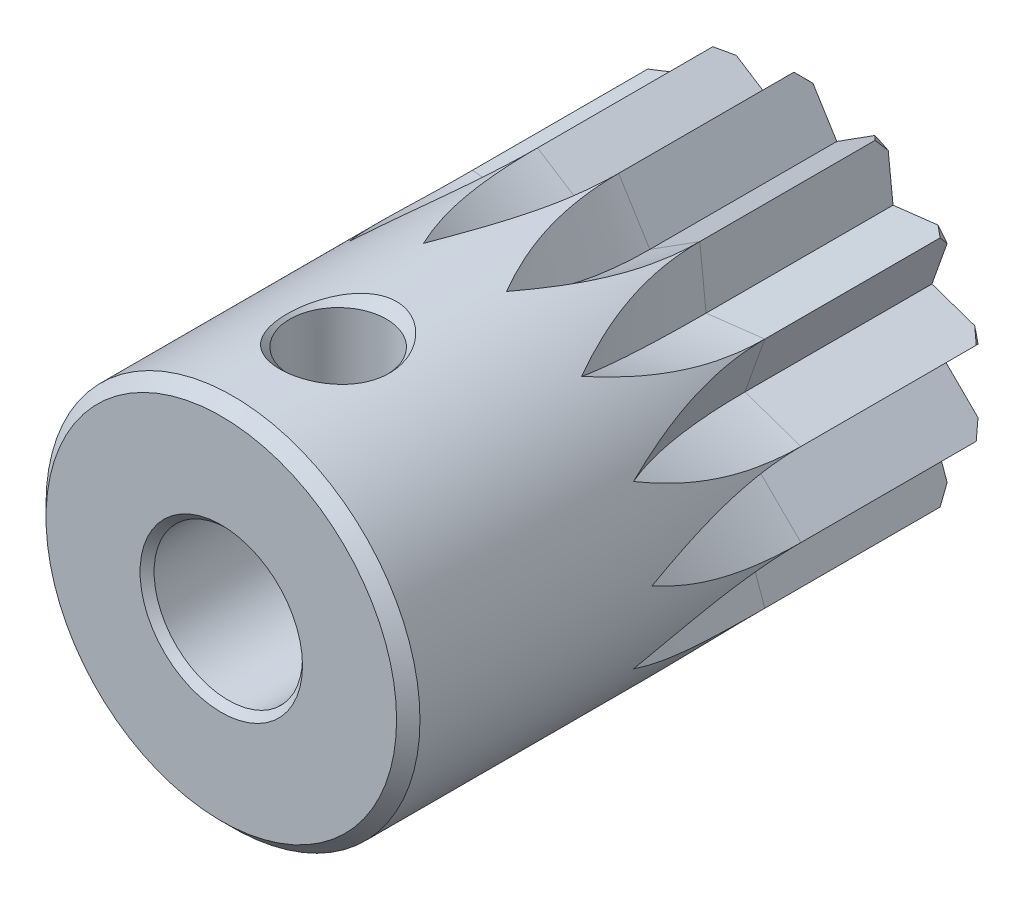
SolidWorks part; units mm, degrees
ref_plane "Front Plane" through (0, 0, 0) normal (0, 0, 1) x (1, 0, 0)
ref_plane "Top Plane" through (0, 0, 0) normal (0, 1, 0) x (1, 0, 0)
ref_plane "Right Plane" through (0, 0, 0) normal (1, 0, 0) x (0, 0, -1)
ref_plane "Plane1" through (0, 0, 0) normal (1, 0, 0) x (0, 0, -1)
sketch "Sketch1" plane through (0, 0, 0) normal (1, 0, 0) x (0, 0, -1)
  line L0 (-25, 3.475) -> (-24.7, 3.175)
  line L1 (-24.7, 3.175) -> (-0.3, 3.175)
  line L2 (-0.3, 3.175) -> (0, 3.475)
  line L3 (0, 3.475) -> (0, 7.5)
  line L4 (0, 7.5) -> (-0.5, 8)
  line L5 (-0.5, 8) -> (-24.5, 8)
  line L6 (-24.5, 8) -> (-25, 7.5)
  line L7 (-25, 7.5) -> (-25, 3.475)
  line L8 (0, 0) -> (-25, 0) construction
revolve "Revolve1" add sketch "Sketch1" angle 360 about L8
ref_plane "Plane2" through (0, 0, 8) normal (0, 0, 1) x (1, 0, 0)
sketch "Sketch2" plane through (0, 0, 8) normal (0, 0, 1) x (1, 0, 0)
  line L0 (-7.7994, 1.7802) -> (-6, 0)
  line L1 (-6, 0) -> (-7.7994, -1.7802)
  line L2 (-7.7994, -1.7802) -> (-5.4058, -2.6033)
  line L3 (-5.4058, -2.6033) -> (-6.2547, -4.9879)
  line L4 (-6.2547, -4.9879) -> (-3.7409, -4.691)
  line L5 (-3.7409, -4.691) -> (-3.4711, -7.2078)
  line L6 (-3.4711, -7.2078) -> (-1.3351, -5.8496)
  line L7 (-1.3351, -5.8496) -> (0, -8)
  line L8 (0, -8) -> (1.3351, -5.8496)
  line L9 (1.3351, -5.8496) -> (3.4711, -7.2078)
  line L10 (3.4711, -7.2078) -> (3.7409, -4.691)
  line L11 (3.7409, -4.691) -> (6.2547, -4.9879)
  line L12 (6.2547, -4.9879) -> (5.4058, -2.6033)
  line L13 (5.4058, -2.6033) -> (7.7994, -1.7802)
  line L14 (7.7994, -1.7802) -> (6, 0)
  line L15 (6, 0) -> (7.7994, 1.7802)
  line L16 (7.7994, 1.7802) -> (5.4058, 2.6033)
  line L17 (5.4058, 2.6033) -> (6.2547, 4.9879)
  line L18 (6.2547, 4.9879) -> (3.7409, 4.691)
  line L19 (3.7409, 4.691) -> (3.4711, 7.2078)
  line L20 (3.4711, 7.2078) -> (1.3351, 5.8496)
  line L21 (1.3351, 5.8496) -> (0, 8)
  line L22 (0, 8) -> (-1.3351, 5.8496)
  line L23 (-1.3351, 5.8496) -> (-3.4711, 7.2078)
  line L24 (-3.4711, 7.2078) -> (-3.7409, 4.691)
  line L25 (-3.7409, 4.691) -> (-6.2547, 4.9879)
  line L26 (-6.2547, 4.9879) -> (-5.4058, 2.6033)
  line L27 (-5.4058, 2.6033) -> (-7.7994, 1.7802)
  circle A0 centre (0, 0) radius 16
extrude "Cut-Extrude1" cut sketch "Sketch2" against normal blind 8
ref_plane "Plane3" through (0, 0, 8) normal (0, 0, 1) x (1, 0, 0)
sketch "Sketch3" plane through (0, 0, 8) normal (0, 0, 1) x (1, 0, 0)
  line L0 (-2.2252, 17.7493) -> (0, 8)
  line L1 (0, 8) -> (-1.3351, 5.8496)
  line L2 (-1.3351, 5.8496) -> (-3.4711, 7.2078)
  line L3 (-3.4711, 7.2078) -> (-5.6963, 16.957)
  line L4 (-5.6963, 16.957) -> (-2.2252, 17.7493)
  line L5 (-5.6963, 16.957) -> (-2.2252, 17.7493) construction
revolve "Cut-Revolve1" cut sketch "Sketch3" angle 360 about L5
ref_plane "Plane4" through (0, 0, 8) normal (0, 0, 1) x (1, 0, 0)
sketch "Sketch4" plane through (0, 0, 8) normal (0, 0, 1) x (1, 0, 0)
  line L0 (5.6963, 16.957) -> (3.4711, 7.2078)
  line L1 (3.4711, 7.2078) -> (1.3351, 5.8496)
  line L2 (1.3351, 5.8496) -> (0, 8)
  line L3 (0, 8) -> (2.2252, 17.7493)
  line L4 (2.2252, 17.7493) -> (5.6963, 16.957)
  line L5 (2.2252, 17.7493) -> (5.6963, 16.957) construction
revolve "Cut-Revolve2" cut sketch "Sketch4" angle 360 about L5
ref_plane "Plane5" through (0, 0, 8) normal (0, 0, 1) x (1, 0, 0)
sketch "Sketch5" plane through (0, 0, 8) normal (0, 0, 1) x (1, 0, 0)
  line L0 (12.4895, 12.8062) -> (6.2547, 4.9879)
  line L1 (6.2547, 4.9879) -> (3.7409, 4.691)
  line L2 (3.7409, 4.691) -> (3.4711, 7.2078)
  line L3 (3.4711, 7.2078) -> (9.706, 15.0261)
  line L4 (9.706, 15.0261) -> (12.4895, 12.8062)
  line L5 (9.706, 15.0261) -> (12.4895, 12.8062) construction
revolve "Cut-Revolve3" cut sketch "Sketch5" angle 360 about L5
ref_plane "Plane6" through (0, 0, 8) normal (0, 0, 1) x (1, 0, 0)
sketch "Sketch6" plane through (0, 0, 8) normal (0, 0, 1) x (1, 0, 0)
  line L0 (16.8091, 6.119) -> (7.7994, 1.7802)
  line L1 (7.7994, 1.7802) -> (5.4058, 2.6033)
  line L2 (5.4058, 2.6033) -> (6.2547, 4.9879)
  line L3 (6.2547, 4.9879) -> (15.2643, 9.3268)
  line L4 (15.2643, 9.3268) -> (16.8091, 6.119)
  line L5 (15.2643, 9.3268) -> (16.8091, 6.119) construction
revolve "Cut-Revolve4" cut sketch "Sketch6" angle 360 about L5
ref_plane "Plane7" through (0, 0, 8) normal (0, 0, 1) x (1, 0, 0)
sketch "Sketch7" plane through (0, 0, 8) normal (0, 0, 1) x (1, 0, 0)
  line L0 (17.7994, -1.7802) -> (7.7994, -1.7802)
  line L1 (7.7994, -1.7802) -> (6, 0)
  line L2 (6, 0) -> (7.7994, 1.7802)
  line L3 (7.7994, 1.7802) -> (17.7994, 1.7802)
  line L4 (17.7994, 1.7802) -> (17.7994, -1.7802)
  line L5 (17.7994, 1.7802) -> (17.7994, -1.7802) construction
revolve "Cut-Revolve5" cut sketch "Sketch7" angle 360 about L5
ref_plane "Plane8" through (0, 0, 8) normal (0, 0, 1) x (1, 0, 0)
sketch "Sketch8" plane through (0, 0, 8) normal (0, 0, 1) x (1, 0, 0)
  line L0 (15.2643, -9.3268) -> (6.2547, -4.9879)
  line L1 (6.2547, -4.9879) -> (5.4058, -2.6033)
  line L2 (5.4058, -2.6033) -> (7.7994, -1.7802)
  line L3 (7.7994, -1.7802) -> (16.8091, -6.119)
  line L4 (16.8091, -6.119) -> (15.2643, -9.3268)
  line L5 (16.8091, -6.119) -> (15.2643, -9.3268) construction
revolve "Cut-Revolve6" cut sketch "Sketch8" angle 360 about L5
ref_plane "Plane9" through (0, 0, 8) normal (0, 0, 1) x (1, 0, 0)
sketch "Sketch9" plane through (0, 0, 8) normal (0, 0, 1) x (1, 0, 0)
  line L0 (9.706, -15.0261) -> (3.4711, -7.2078)
  line L1 (3.4711, -7.2078) -> (3.7409, -4.691)
  line L2 (3.7409, -4.691) -> (6.2547, -4.9879)
  line L3 (6.2547, -4.9879) -> (12.4895, -12.8062)
  line L4 (12.4895, -12.8062) -> (9.706, -15.0261)
  line L5 (12.4895, -12.8062) -> (9.706, -15.0261) construction
revolve "Cut-Revolve7" cut sketch "Sketch9" angle 360 about L5
ref_plane "Plane10" through (0, 0, 8) normal (0, 0, 1) x (1, 0, 0)
sketch "Sketch10" plane through (0, 0, 8) normal (0, 0, 1) x (1, 0, 0)
  line L0 (2.2252, -17.7493) -> (0, -8)
  line L1 (0, -8) -> (1.3351, -5.8496)
  line L2 (1.3351, -5.8496) -> (3.4711, -7.2078)
  line L3 (3.4711, -7.2078) -> (5.6963, -16.957)
  line L4 (5.6963, -16.957) -> (2.2252, -17.7493)
  line L5 (5.6963, -16.957) -> (2.2252, -17.7493) construction
revolve "Cut-Revolve8" cut sketch "Sketch10" angle 360 about L5
ref_plane "Plane11" through (0, 0, 8) normal (0, 0, 1) x (1, 0, 0)
sketch "Sketch11" plane through (0, 0, 8) normal (0, 0, 1) x (1, 0, 0)
  line L0 (-5.6963, -16.957) -> (-3.4711, -7.2078)
  line L1 (-3.4711, -7.2078) -> (-1.3351, -5.8496)
  line L2 (-1.3351, -5.8496) -> (0, -8)
  line L3 (0, -8) -> (-2.2252, -17.7493)
  line L4 (-2.2252, -17.7493) -> (-5.6963, -16.957)
  line L5 (-2.2252, -17.7493) -> (-5.6963, -16.957) construction
revolve "Cut-Revolve9" cut sketch "Sketch11" angle 360 about L5
ref_plane "Plane12" through (0, 0, 8) normal (0, 0, 1) x (1, 0, 0)
sketch "Sketch12" plane through (0, 0, 8) normal (0, 0, 1) x (1, 0, 0)
  line L0 (-12.4895, -12.8062) -> (-6.2547, -4.9879)
  line L1 (-6.2547, -4.9879) -> (-3.7409, -4.691)
  line L2 (-3.7409, -4.691) -> (-3.4711, -7.2078)
  line L3 (-3.4711, -7.2078) -> (-9.706, -15.0261)
  line L4 (-9.706, -15.0261) -> (-12.4895, -12.8062)
  line L5 (-9.706, -15.0261) -> (-12.4895, -12.8062) construction
revolve "Cut-Revolve10" cut sketch "Sketch12" angle 360 about L5
ref_plane "Plane13" through (0, 0, 8) normal (0, 0, 1) x (1, 0, 0)
sketch "Sketch13" plane through (0, 0, 8) normal (0, 0, 1) x (1, 0, 0)
  line L0 (-16.8091, -6.119) -> (-7.7994, -1.7802)
  line L1 (-7.7994, -1.7802) -> (-5.4058, -2.6033)
  line L2 (-5.4058, -2.6033) -> (-6.2547, -4.9879)
  line L3 (-6.2547, -4.9879) -> (-15.2643, -9.3268)
  line L4 (-15.2643, -9.3268) -> (-16.8091, -6.119)
  line L5 (-15.2643, -9.3268) -> (-16.8091, -6.119) construction
revolve "Cut-Revolve11" cut sketch "Sketch13" angle 360 about L5
ref_plane "Plane14" through (0, 0, 8) normal (0, 0, 1) x (1, 0, 0)
sketch "Sketch14" plane through (0, 0, 8) normal (0, 0, 1) x (1, 0, 0)
  line L0 (-17.7994, 1.7802) -> (-7.7994, 1.7802)
  line L1 (-7.7994, 1.7802) -> (-6, 0)
  line L2 (-6, 0) -> (-7.7994, -1.7802)
  line L3 (-7.7994, -1.7802) -> (-17.7994, -1.7802)
  line L4 (-17.7994, -1.7802) -> (-17.7994, 1.7802)
  line L5 (-17.7994, -1.7802) -> (-17.7994, 1.7802) construction
revolve "Cut-Revolve12" cut sketch "Sketch14" angle 360 about L5
ref_plane "Plane15" through (0, 0, 8) normal (0, 0, 1) x (1, 0, 0)
sketch "Sketch15" plane through (0, 0, 8) normal (0, 0, 1) x (1, 0, 0)
  line L0 (-15.2643, 9.3268) -> (-6.2547, 4.9879)
  line L1 (-6.2547, 4.9879) -> (-5.4058, 2.6033)
  line L2 (-5.4058, 2.6033) -> (-7.7994, 1.7802)
  line L3 (-7.7994, 1.7802) -> (-16.8091, 6.119)
  line L4 (-16.8091, 6.119) -> (-15.2643, 9.3268)
  line L5 (-16.8091, 6.119) -> (-15.2643, 9.3268) construction
revolve "Cut-Revolve13" cut sketch "Sketch15" angle 360 about L5
ref_plane "Plane16" through (0, 0, 8) normal (0, 0, 1) x (1, 0, 0)
sketch "Sketch16" plane through (0, 0, 8) normal (0, 0, 1) x (1, 0, 0)
  line L0 (-9.706, 15.0261) -> (-3.4711, 7.2078)
  line L1 (-3.4711, 7.2078) -> (-3.7409, 4.691)
  line L2 (-3.7409, 4.691) -> (-6.2547, 4.9879)
  line L3 (-6.2547, 4.9879) -> (-12.4895, 12.8062)
  line L4 (-12.4895, 12.8062) -> (-9.706, 15.0261)
  line L5 (-12.4895, 12.8062) -> (-9.706, 15.0261) construction
revolve "Cut-Revolve14" cut sketch "Sketch16" angle 360 about L5
ref_plane "Plane17" through (0, 0, 20) normal (0, 0, 1) x (1, 0, 0)
sketch "Sketch17" plane through (0, 0, 20) normal (0, 0, 1) x (1, 0, 0)
  line L0 (0, 0) -> (-2.067, 0)
  line L1 (-2.067, 0) -> (-2.067, 7.567)
  line L2 (-2.067, 7.567) -> (-2.5, 8)
  line L3 (-2.5, 8) -> (-2.5, 9)
  line L4 (-2.5, 9) -> (0, 9)
  line L5 (0, 9) -> (0, 0)
  line L6 (0, 9) -> (0, 0) construction
revolve "Cut-Revolve15" cut sketch "Sketch17" angle 360 about L6
